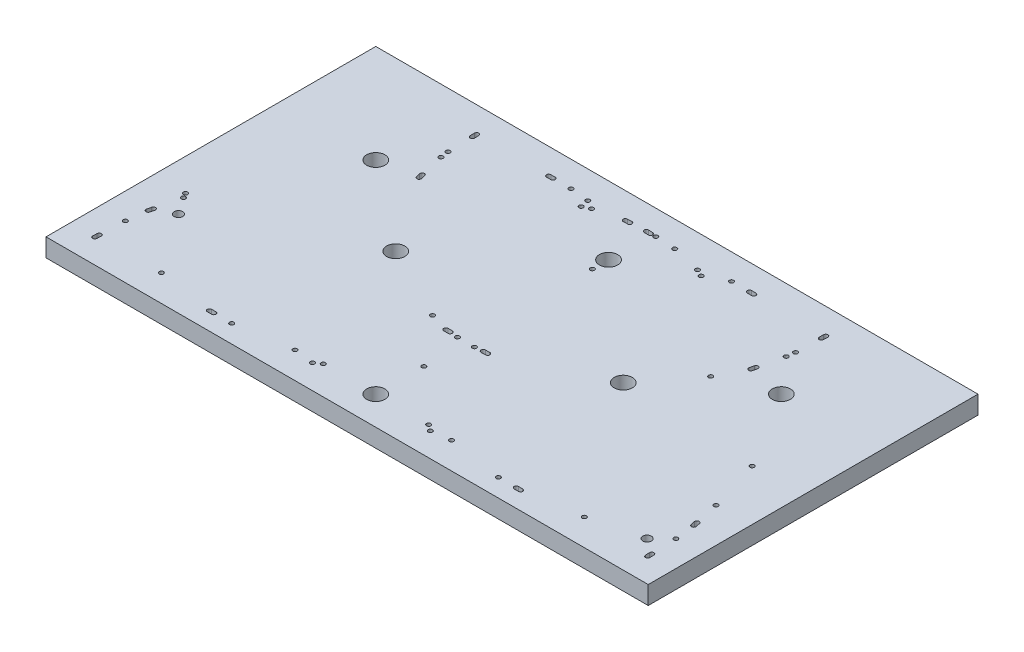
SolidWorks part; units mm, degrees
ref_plane "Front Plane" through (0, 0, 0) normal (0, 0, 1) x (1, 0, 0)
ref_plane "Top Plane" through (0, 0, 0) normal (0, 1, 0) x (1, 0, 0)
ref_plane "Right Plane" through (0, 0, 0) normal (1, 0, 0) x (0, 0, -1)
sketch "Sketch1" plane through (0, 0, 0) normal (0, 1, 0) x (1, 0, 0)
  line L0 (212.5, 0) -> (212.5, 230) construction
  line L1 (0, 0) -> (420, 0)
  line L2 (0, 0) -> (0, 230)
  line L3 (0, 230) -> (420, 230)
  line L4 (420, 0) -> (420, 230)
extrude "Boss-Extrude1" add sketch "Sketch1" along normal blind 12.7
sketch "Sketch3" plane through (0, 12.7, 0) normal (0, 1, 0) x (-1, 0, 0)
  line L0 (-210, 0) -> (-210, -230) construction
sketch "Sketch7" plane through (196.4605, 12.7, -62.603) normal (0, 1, 0) x (0.0903, 0, 0.9959)
  line L4 (60.9136, 117.0192) -> (60.6428, 114.0315) construction
  line L5 (62.4075, 116.8838) -> (62.1367, 113.8961)
  line L6 (59.4197, 117.1546) -> (59.149, 114.1668)
  line L7 (41.3276, -99.0951) -> (41.5983, -96.1073) construction
  line L8 (39.8337, -98.9597) -> (40.1045, -95.9719)
  line L9 (42.8214, -99.2305) -> (43.0922, -96.2427)
  line L10 (29.4308, 201.9279) -> (26.4565, 201.5363) construction
  line L11 (29.6266, 200.4408) -> (26.6523, 200.0492)
  line L12 (29.235, 203.4151) -> (26.2607, 203.0235)
  line L13 (-148.6979, 23.0202) -> (-148.3193, 25.9963) construction
  line L14 (-150.1859, 23.2095) -> (-149.8073, 26.1856)
  line L15 (-147.2099, 22.8309) -> (-146.8313, 25.807)
  line L16 (29.4308, -182.6499) -> (26.4565, -182.2583) construction
  line L17 (29.235, -184.1371) -> (26.2607, -183.7455)
  line L18 (29.6266, -181.1628) -> (26.6523, -180.7712)
  line L21 (64.2321, 201.3494) -> (61.236, 201.5031) construction
  line L22 (64.1552, 199.8514) -> (61.1592, 200.005)
  line L23 (64.3089, 202.8474) -> (61.3129, 203.0011)
  line L24 (-149.1576, 9.0884) -> (-149.0039, 12.0844) construction
  line L25 (-150.6556, 9.1652) -> (-150.5019, 12.1613)
  line L26 (-147.6595, 9.0115) -> (-147.5059, 12.0076)
  line L27 (-4.9072, -176.9604) -> (-7.7627, -176.0405) construction
  line L28 (-5.3671, -178.3881) -> (-8.2226, -177.4682)
  line L29 (-4.4472, -175.5327) -> (-7.3027, -174.6127)
  circle A0 centre (43.6512, 9.639) radius 6.35
  circle A1 centre (-109.9574, -118.4407) radius 6.35
  circle A2 centre (43.0997, -31.5081) radius 1.5
  circle A3 centre (9.1062, -179.9741) radius 1.5
  arc A4 (62.4075, 116.8838) -> (59.4197, 117.1546) centre (60.9136, 117.0192) ccw
  circle A5 centre (42.7266, -83.6583) radius 1.5
  circle A6 centre (59.5146, 101.5825) radius 1.5
  arc A7 (39.8337, -98.9597) -> (42.8214, -99.2305) centre (41.3276, -99.0951) ccw
  arc A8 (59.149, 114.1668) -> (62.1367, 113.8961) centre (60.6428, 114.0315) ccw
  circle A9 centre (9.1062, 199.2521) radius 1.5
  circle A10 centre (-146.1109, 43.3563) radius 1.5
  circle A11 centre (46.9861, 46.3699) radius 1.5
  circle A12 centre (31.779, -137.979) radius 1.5
  circle A13 centre (40.196, -45.105) radius 1.5
  circle A14 centre (50.0404, 63.5195) radius 1.5
  circle A15 centre (58.4046, 155.8101) radius 1.5
  circle A16 centre (10.2879, 12.6627) radius 1.5
  circle A17 centre (40.3591, -26.8593) radius 1.5
  circle A18 centre (50.5266, 50.3711) radius 1.5
  circle A20 centre (-84.4285, 163.2476) radius 6.35
  circle A21 centre (-27.9998, 191.5356) radius 1.5
  circle A22 centre (-150.1763, -15.8789) radius 1.5
  circle A23 centre (-27.9998, -172.2576) radius 1.5
  circle A24 centre (-12.1575, -163.5932) radius 3
  circle A25 centre (52.7225, 191.4128) radius 3
  arc A26 (43.0922, -96.2427) -> (40.1045, -95.9719) centre (41.5983, -96.1073) ccw
  arc A27 (29.6266, 200.4408) -> (29.235, 203.4151) centre (29.4308, 201.9279) ccw
  arc A28 (26.2607, 203.0235) -> (26.6523, 200.0492) centre (26.4565, 201.5363) ccw
  arc A29 (-150.1859, 23.2095) -> (-147.2099, 22.8309) centre (-148.6979, 23.0202) ccw
  arc A30 (-146.8313, 25.807) -> (-149.8073, 26.1856) centre (-148.3193, 25.9963) ccw
  arc A31 (29.235, -184.1371) -> (29.6266, -181.1628) centre (29.4308, -182.6499) ccw
  arc A32 (26.6523, -180.7712) -> (26.2607, -183.7455) centre (26.4565, -182.2583) ccw
  circle A34 centre (-24.4196, -170.6742) radius 1.5
  circle A35 centre (-148.0509, 29.5585) radius 1.5
  circle A37 centre (43.7577, 202.3732) radius 1.5
  arc A39 (64.1552, 199.8514) -> (64.3089, 202.8474) centre (64.2321, 201.3494) ccw
  arc A40 (61.3129, 203.0011) -> (61.1592, 200.005) centre (61.236, 201.5031) ccw
  arc A41 (-150.6556, 9.1652) -> (-147.6595, 9.0115) centre (-149.1576, 9.0884) ccw
  arc A42 (-147.5059, 12.0076) -> (-150.5019, 12.1613) centre (-149.0039, 12.0844) ccw
  arc A43 (-5.3671, -178.3881) -> (-4.4472, -175.5327) centre (-4.9072, -176.9604) ccw
  arc A44 (-7.3027, -174.6127) -> (-8.2226, -177.4682) centre (-7.7627, -176.0405) ccw
  point P17 (60.7782, 115.5253)
  point P64 (41.463, -97.6012)
  point P71 (27.9436, 201.7321)
  point P78 (-148.5086, 24.5083)
  point P85 (27.9436, -182.4541)
  point P108 (62.734, 201.4262)
  point P115 (-149.0807, 10.5864)
  point P122 (-6.3349, -176.5004)
sketch "Sketch8" plane through (196.4605, 12.7, -62.603) normal (0, 1, 0) x (0.0903, 0, 0.9959)
  line L2 (-154.1182, -44.2305) -> (-153.8474, -41.2428) construction
  line L3 (-155.6121, -44.0952) -> (-155.3413, -41.1074)
  line L4 (-152.6243, -44.3659) -> (-152.3535, -41.3782)
  line L5 (-141.2112, 98.1858) -> (-141.482, 95.198) construction
  line L6 (-139.7174, 98.0504) -> (-139.9881, 95.0626)
  line L7 (-142.7051, 98.3212) -> (-142.9759, 95.3334)
  line L8 (-136.6284, 148.2455) -> (-133.6498, 147.8877) construction
  line L9 (-136.4495, 149.7348) -> (-133.471, 149.377)
  line L10 (-136.8073, 146.7562) -> (-133.8287, 146.3984)
  line L11 (-91.195, 138.0245) -> (-94.0398, 138.9769) construction
  line L12 (-91.6712, 136.6021) -> (-94.516, 137.5544)
  line L13 (-90.7188, 139.447) -> (-93.5637, 140.3993)
  line L14 (-20.874, 0.8907) -> (-20.5162, 3.8693) construction
  line L15 (-22.3633, 1.0696) -> (-22.0055, 4.0482)
  line L16 (-19.3847, 0.7119) -> (-19.0269, 3.6905)
  line L17 (-18.2499, 29.845) -> (-18.4335, 26.8507) construction
  line L18 (-16.7527, 29.7533) -> (-16.9363, 26.7589)
  line L19 (-19.7471, 29.9368) -> (-19.9307, 26.9425)
  line L20 (-158.6097, -94.2985) -> (-155.6154, -94.4821) construction
  line L21 (-158.518, -92.8013) -> (-155.5236, -92.9849)
  line L22 (-158.7015, -95.7957) -> (-155.7072, -95.9792)
  line L23 (-112.0791, -92.4121) -> (-115.0488, -92.8375) construction
  line L24 (-111.8664, -93.8969) -> (-114.8361, -94.3223)
  line L25 (-112.2918, -90.9273) -> (-115.2615, -91.3526)
  circle A0 centre (-136.6725, 68.2117) radius 1.5
  circle A1 centre (-138.1482, -95.5529) radius 1.5
  circle A2 centre (-117.9973, 24.2889) radius 6.35
  circle A3 centre (-146.0728, -10.0574) radius 1.5
  circle A4 centre (-152.7192, -28.7938) radius 1.5
  circle A5 centre (-25.9279, -11.9511) radius 1.5
  circle A6 centre (-19.5044, 9.3835) radius 1.5
  circle A7 centre (-42.0269, 97.0792) radius 6.35
  circle A8 centre (-73.6723, 126.7743) radius 1.5
  circle A9 centre (-56.3509, -60.9733) radius 6.35
  circle A10 centre (-110.6347, 144.5321) radius 1.5
  circle A12 centre (-142.6103, 82.7491) radius 1.5
  circle A13 centre (-106.8321, 23.277) radius 1.5
  circle A14 centre (-144.2419, -15.1909) radius 1.5
  circle A15 centre (-139.4151, 63.5397) radius 1.5
  circle A18 centre (-116.2747, 145.8009) radius 1.5
  circle A19 centre (-18.4294, 21.2445) radius 1.5
  circle A21 centre (-132.372, -95.3188) radius 1.5
  arc A23 (-155.6121, -44.0952) -> (-152.6243, -44.3659) centre (-154.1182, -44.2305) ccw
  arc A24 (-152.3535, -41.3782) -> (-155.3413, -41.1074) centre (-153.8474, -41.2428) ccw
  arc A25 (-139.7174, 98.0504) -> (-142.7051, 98.3212) centre (-141.2112, 98.1858) ccw
  arc A26 (-142.9759, 95.3334) -> (-139.9881, 95.0626) centre (-141.482, 95.198) ccw
  arc A27 (-136.4495, 149.7348) -> (-136.8073, 146.7562) centre (-136.6284, 148.2455) ccw
  arc A28 (-133.8287, 146.3984) -> (-133.471, 149.377) centre (-133.6498, 147.8877) ccw
  arc A29 (-91.6712, 136.6021) -> (-90.7188, 139.447) centre (-91.195, 138.0245) ccw
  arc A30 (-93.5637, 140.3993) -> (-94.516, 137.5544) centre (-94.0398, 138.9769) ccw
  arc A31 (-22.3633, 1.0696) -> (-19.3847, 0.7119) centre (-20.874, 0.8907) ccw
  arc A32 (-19.0269, 3.6905) -> (-22.0055, 4.0482) centre (-20.5162, 3.8693) ccw
  arc A33 (-16.7527, 29.7533) -> (-19.7471, 29.9368) centre (-18.2499, 29.845) ccw
  arc A34 (-19.9307, 26.9425) -> (-16.9363, 26.7589) centre (-18.4335, 26.8507) ccw
  arc A35 (-158.518, -92.8013) -> (-158.7015, -95.7957) centre (-158.6097, -94.2985) ccw
  arc A36 (-155.7072, -95.9792) -> (-155.5236, -92.9849) centre (-155.6154, -94.4821) ccw
  arc A37 (-111.8664, -93.8969) -> (-112.2918, -90.9273) centre (-112.0791, -92.4121) ccw
  arc A38 (-115.2615, -91.3526) -> (-114.8361, -94.3223) centre (-115.0488, -92.8375) ccw
  point P53 (-153.9828, -42.7367)
  point P60 (-141.3466, 96.6919)
  point P67 (-135.1391, 148.0666)
  point P74 (-92.6174, 138.5007)
  point P81 (-20.6951, 2.38)
  point P88 (-18.3417, 28.3479)
  point P95 (-157.1126, -94.3903)
  point P102 (-113.5639, -92.6248)
extrude "Cut-Extrude1" cut sketch "Sketch7" against normal blind 12.7
extrude "Cut-Extrude2" cut sketch "Sketch8" against normal blind 12.7
